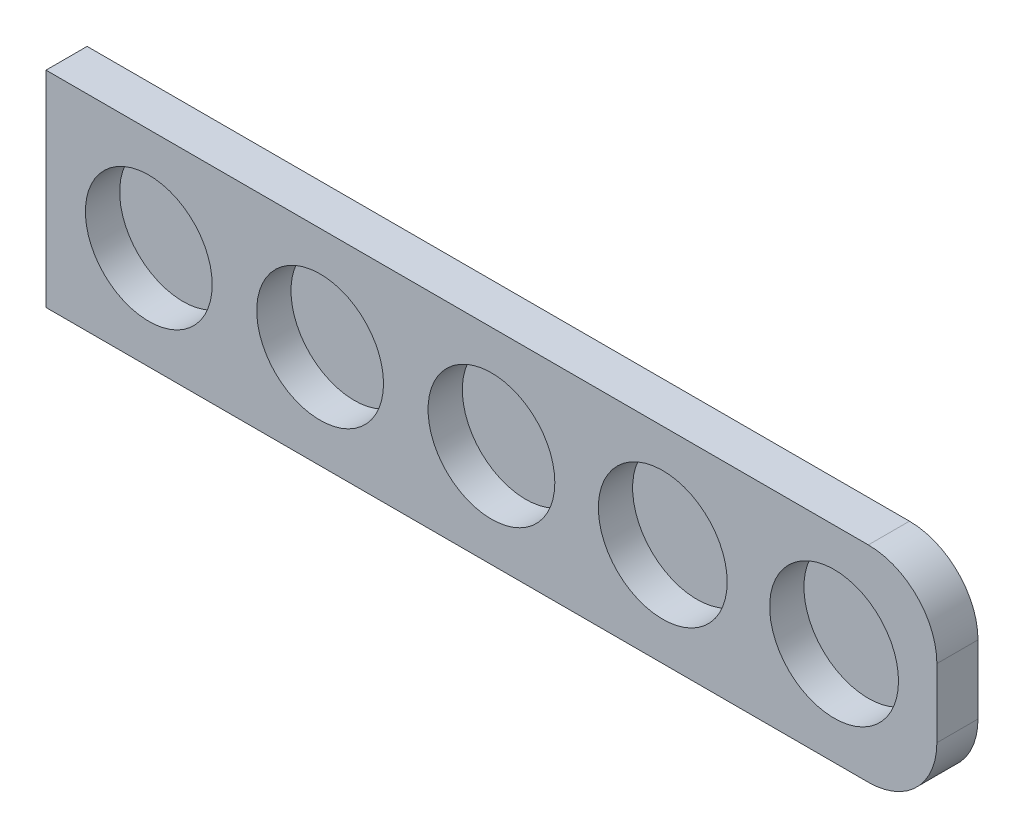
SolidWorks part; units mm, degrees
ref_plane "前视基准面" through (0, 0, 0) normal (0, 0, 1) x (1, 0, 0)
ref_plane "上视基准面" through (0, 0, 0) normal (0, 1, 0) x (1, 0, 0)
ref_plane "右视基准面" through (0, 0, 0) normal (1, 0, 0) x (0, 0, -1)
ref_plane "基准面4" through (0, 0, 0) normal (0, 0, -1) x (-1, 0, 0)
sketch "草图1" plane through (0, 0, 0) normal (0, 0, -1) x (-1, 0, 0)
  line L0 (-130, -56) -> (-130, -86)
  line L1 (-130, -86) -> (0, -86)
  line L2 (0, -86) -> (0, -56)
  line L3 (0, -56) -> (-130, -56)
extrude "凸台-拉伸1" add sketch "草图1" against normal blind 6
hole_wizard "M16 间隙孔1" positions "草图3" profile "草图2" hole size "M16" standard "ANSI Metric"
sketch "草图3" plane through (0, 0, 6) normal (0, 0, 1) x (1, 0, 0)
  point P0 (90, -71)
  point P1 (115, -71)
sketch "草图2" plane through (90, -71, 6) normal (1, 0, 0) x (0, -1, 0)
  line L0 (0, 0) -> (0, 5)
  line L1 (0, 5) -> (9.4, 5)
  line L2 (9.4, 5) -> (9.4, 0)
  line L5 (9.4, 0) -> (0, 0)
  line L10 (0, 5) -> (-9.4, 5) construction
  line L11 (0, -6.35) -> (0, 107.95) construction
  dimension "孔直径" = 18.8
  dimension "孔深度" = 5
  dimension "导头角度" = 180
hole_wizard "Ø18.5 (18.5) 直径孔1" positions "草图5" profile "草图4" hole size "Ø18.5" standard "ANSI Metric"
sketch "草图5" plane through (0, 0, 6) normal (0, 0, 1) x (1, 0, 0)
  point P0 (15, -71)
  point P1 (40, -71)
  point P2 (65, -71)
sketch "草图4" plane through (15, -71, 6) normal (1, 0, 0) x (0, -1, 0)
  line L0 (0, 0) -> (0, 5)
  line L1 (0, 5) -> (9.25, 5)
  line L2 (9.25, 5) -> (9.25, 0)
  line L5 (9.25, 0) -> (0, 0)
  line L10 (0, 5) -> (-9.25, 5) construction
  line L11 (0, -6.35) -> (0, 107.95) construction
  dimension "孔直径" = 18.5
  dimension "孔深度" = 5
  dimension "导头角度" = 180
fillet "圆角1" radius 10 2 edges at (130, -56, 3) (130, -86, 3)
